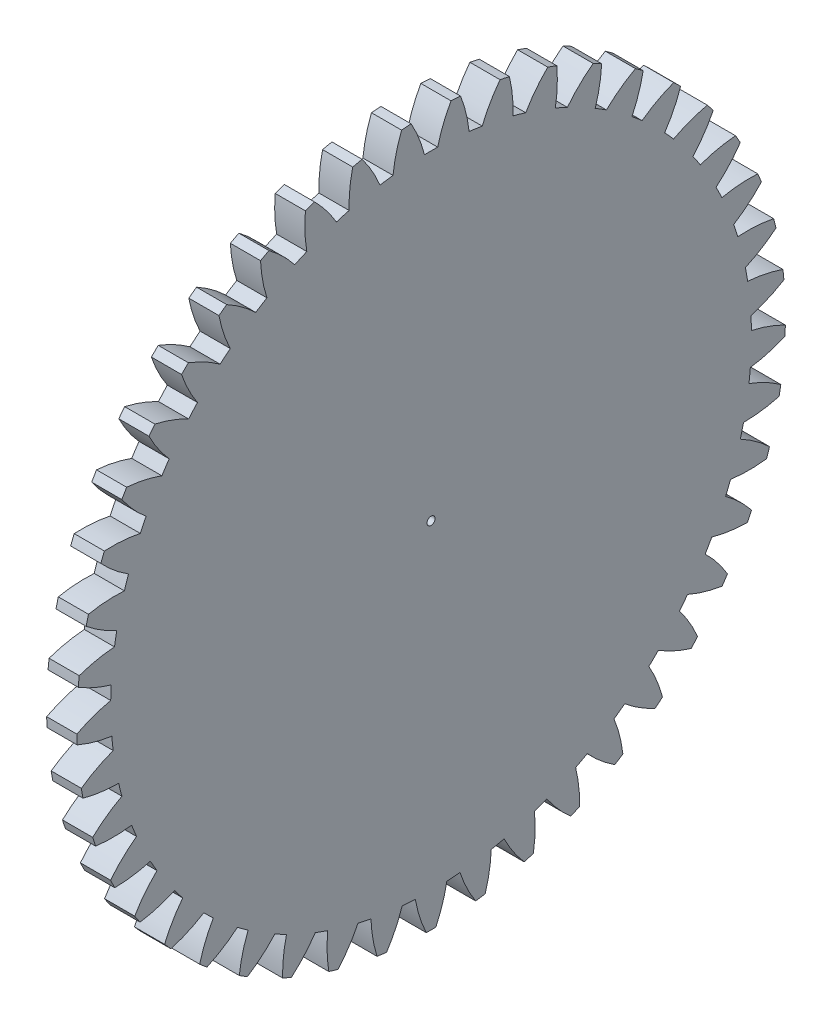
SolidWorks part; units mm, degrees
ref_plane "Plane1" through (0, 0, 0) normal (0, 0, 1) x (1, 0, 0)
ref_plane "Plane2" through (0, 0, 0) normal (0, 1, 0) x (1, 0, 0)
ref_plane "Plane3" through (0, 0, 0) normal (1, 0, 0) x (0, 0, -1)
sketch "HoldingSke" plane through (0, 0, 0) normal (0, 1, 0) x (1, 0, 0)
  line L0 (0, 0) -> (0.4714, -0.4714)
  line L1 (-15, 0) -> (100, 0) construction
  line L2 (0, 0) -> (-2.1039, 2.3779)
  line L3 (0, 0) -> (-11.863, 4.5341)
  line L4 (0, 0) -> (6.1066, 6.1066)
  line L5 (0, 0) -> (-46.8476, -17.4728)
  line L6 (0, 0) -> (-2.4869, -1.6779)
  line L7 (-2.1039, 2.3779) -> (8.6586, 51.2059)
  line L8 (-76.2, 54.61) -> (-76.1, 54.61)
  line L9 (-71.009, 38.7566) -> (-53.1078, 45.2721)
  line L10 (-76.2, 71.12) -> (104.1128, 71.12)
  line L11 (0, 0) -> (-3, 0)
  line L12 (-76.2, 101.6) -> (-76.147, 101.6)
  line L13 (24.9733, 27.94) -> (52.9518, 28.4284)
  line L14 (24.9733, 27.94) -> (24.9743, 27.94)
  line L15 (24.9733, 27.94) -> (100.4006, 29.5858)
  line L16 (-63.627, -1.5) -> (-12.827, -1.5)
  circle A0 centre (0, 0) radius 0.4
  circle A1 centre (0, 0) radius 31.874
  circle A2 centre (0, 0) radius 37.5
  circle A3 centre (0, 0) radius 0.4
  dimension "MHD" = 63.748
  dimension "Hub_dia" = 75
  dimension "Bore" = 0.8
  dimension "MBD" = 0.8
  dimension "Num_teeth" = 45
  dimension "Pitch" = 0.6667
  dimension "Overall_len" = 50
  dimension "Show_teeth" = 45
  dimension "Thickness" = 3
  dimension "OAL" = 50.0001
  dimension "T_dim" = 0.1
  dimension "Ap" = 20
  dimension "H" = 19.05
  dimension "Pitch_radius" = 180.3128
  dimension "Width" = 3
  dimension "Backlash" = 0.053
  dimension "Addendum_fac" = 1
  dimension "Dedendum_fac" = 1.25
  dimension "Clearance_fac" = 0.25
  dimension "Dedendum_add" = 0.001
  dimension "Module" = 1.5
sketch "BasProSke" plane through (0, 0, 0) normal (0, 1, 0) x (1, 0, 0)
  line L0 (-10, 0) -> (60, 0) construction
  line L1 (0, 0) -> (0, 35.25)
  line L2 (0, 0) -> (3, 0)
  line L3 (3, 0) -> (3, 35.25)
  line L4 (3, 35.25) -> (0, 35.25)
  dimension "Thickness" = 3
  dimension "Diameter" = 70.5
revolve "Base-Revolve" add sketch "BasProSke" angle 360 about L0
sketch "TooCutSke" plane through (0, 0, 0) normal (1, 0, 0) x (0, 0, -1)
  line L1 (0, 0) -> (0, 107) construction
  line L2 (0, 0) -> (-1.2706, 33.7261) construction
  line L3 (0, 0) -> (-4.7061, 67.3008) construction
  line L4 (-1.2706, 33.7261) -> (-2.3531, 33.6504) construction
  arc A0 (0.6574, 31.8672) -> (-0.6574, 31.8672) centre (0, 0) ccw
  arc A1 (1.9967, 35.2188) -> (-1.9967, 35.2188) centre (0, 0) ccw
  circle A2 centre (0, 0) radius 33.75 construction
  circle A3 centre (0, 0) radius 31.7146 construction
  arc A4 (-0.6574, 31.8672) -> (-1.9967, 35.2188) centre (-13.7507, 28.5786) ccw
  arc A5 (1.9967, 35.2188) -> (0.6574, 31.8672) centre (13.7507, 28.5786) ccw
  dimension "Root_dia" = 63.748
  dimension "Overcut_dia" = 70.5508
  dimension "Pitch_dia" = 67.5
  dimension "Base_dia" = 63.4293
  dimension "Flank_rad" = 13.5
  dimension "Half_ang" = 4
  dimension "Half_CT" = 1.0851
extrude "ToothCut" cut sketch "TooCutSke" along normal through all
fillet "Breaks" [suppressed] radius 0.03
fillet "RootFillets" [suppressed] radius 0.376
pattern_circular "TeethCuts" count 45 every 8 about axis through (-10, 0, 0) along (1, 0, 0) of "ToothCut", "RootFillets", "Breaks"
sketch "HubNeaOneSke" plane through (0, 0, 0) normal (-1, 0, 0) x (0, 0, 1)
  circle A0 centre (0, 0) radius 31.874
  dimension "Diameter" = 63.748
extrude "HubNearOne" [suppressed] add sketch "HubNeaOneSke" along normal blind 47.0001
sketch "HubNeaBotSke" plane through (0, 0, 0) normal (-1, 0, 0) x (0, 0, 1)
  circle A0 centre (0, 0) radius 31.874
  dimension "Diameter" = 63.748
extrude "HubNearBoth" [suppressed] add sketch "HubNeaBotSke" along normal blind 23.5
ref_plane "FarPln" through (3, 0, 0) normal (1, 0, 0) x (0, 0, -1)
sketch "HubFarSke" plane through (3, 0, 0) normal (1, 0, 0) x (0, 0, -1)
  circle A0 centre (0, 0) radius 31.874
  dimension "Diameter" = 63.748
extrude "HubFar" [suppressed] add sketch "HubFarSke" along normal blind 23.5
sketch "BorSke" plane through (0, 0, 0) normal (1, 0, 0) x (0, 0, -1)
  circle A0 centre (0, 0) radius 0.4
  dimension "Diameter" = 0.8
extrude "Bore" cut sketch "BorSke" along normal mid plane 100.0001
sketch "KeySke" plane through (0, 0, 0) normal (1, 0, 0) x (0, 0, -1)
  line L0 (-0.05, 0) -> (-0.05, 0.5)
  line L1 (-0.05, 0.5) -> (0.05, 0.5)
  line L2 (0.05, 0.5) -> (0.05, 0)
  line L3 (0, 0) -> (0, 34) construction
  line L4 (-0.05, 0) -> (0.05, 0)
  dimension "Offset" = 0.5
  dimension "Width" = 0.1
extrude "Keyway" [suppressed] cut sketch "KeySke" along normal mid plane 100.0001
pattern_circular "Keyway2" [suppressed] count 2 every 90 about axis through (-10, 0, 0) along (1, 0, 0)
equation "' \"Module@HoldingSke\" = 6.35"
equation "' \"Num_teeth@HoldingSke\" = 12"
equation "' \"Ap@HoldingSke\" =  20"
equation "' \"Ap@HoldingSke\" = 20"
equation "' \"Width@HoldingSke\" = 0.5 * 25.4"
equation "' \"Hub_dia@HoldingSke\"= 1 * 25.4"
equation "' \"Hub_dia@HoldingSke\" = 1 * 25.4"
equation "' \"Overall_len@HoldingSke\" = 1.0 * 25.4"
equation "' \"Bore@HoldingSke\" = 0.75 * 25.4"
equation "' \"T_dim@HoldingSke\" = 0.1 * 25.4"
equation "' \"Width@KeySke\" = 0.25 * 25.4"
equation "' \"Show_teeth@HoldingSke\" = 13"
equation "' \"Backlash@HoldingSke\" = 0.009 * 25.4"
equation "' \"Addendum_fac@HoldingSke\" = 1.0"
equation "' \"Dedendum_fac@HoldingSke\" = 1.25"
equation "' \"Dedendum_add@HoldingSke\" = 0.00005 * 25.4"
equation "' \"Clearance_fac@HoldingSke\" = 0.25"
equation "\"Pitch@HoldingSke\" = 1 / \"Module@HoldingSke\""
equation "\"Overcut_dia@TooCutSke\" = (\"Num_teeth@HoldingSke\" + 2 * \"Addendum_fac@HoldingSke\") / \"Pitch@HoldingSke\" + 0.002 * 25.4"
equation "\"Pitch_dia@TooCutSke\" = \"Num_teeth@HoldingSke\" / \"Pitch@HoldingSke\""
equation "\"Base_dia@TooCutSke\" = \"Num_teeth@HoldingSke\" / \"Pitch@HoldingSke\" * cos((\"Ap@HoldingSke\"  * 3.14159265 / 180))"
equation "\"Root_dia@TooCutSke\" = (\"Num_teeth@HoldingSke\" + 2) / \"Pitch@HoldingSke\" - 2 * (\"Addendum_fac@HoldingSke\" + \"Dedendum_fac@HoldingSke\") / \"Pitch@HoldingSke\" - \"Dedendum_add@HoldingSke\" * 2"
equation "\"Half_ang@TooCutSke\" = 180 / \"Num_teeth@HoldingSke\""
equation "\"Half_CT@TooCutSke\" = \"Num_teeth@HoldingSke\" / \"Pitch@HoldingSke\" * sin((3.14159265 / 2 / \"Num_teeth@HoldingSke\")) / 2 - 7 * \"Backlash@HoldingSke\" / 4"
equation "\"Flank_rad@TooCutSke\" = \"Num_teeth@HoldingSke\" / \"Pitch@HoldingSke\" / 5"
equation "\"Radius@RootFillets\" = \"Clearance_fac@HoldingSke\" / \"Pitch@HoldingSke\" + \"Dedendum_add@HoldingSke\""
equation "\"Break_rad@Breaks\" = 0.02 / \"Pitch@HoldingSke\""
equation "\"Thickness@HoldingSke\" = \"Width@HoldingSke\""
equation "\"OAL@HoldingSke\" = \"Thickness@HoldingSke\""
equation "\"MHD@HoldingSke\" = (\"Num_teeth@HoldingSke\" + 2) / \"Pitch@HoldingSke\" - 2 * (\"Addendum_fac@HoldingSke\" + \"Dedendum_fac@HoldingSke\")  / \"Pitch@HoldingSke\" - \"Dedendum_add@HoldingSke\" * 2"
equation "\"MBD@HoldingSke\" = (\"Num_teeth@HoldingSke\" + 2) / \"Pitch@HoldingSke\" - 2 * (\"Addendum_fac@HoldingSke\" + \"Dedendum_fac@HoldingSke\")  / \"Pitch@HoldingSke\" - \"Dedendum_add@HoldingSke\" * 2 - 0.002 * 25.4"
equation "\"MHD@HoldingSke\" = ((sgn( \"MHD@HoldingSke\" - \"Hub_dia@HoldingSke\" )-1)*( \"MHD@HoldingSke\" - \"Hub_dia@HoldingSke\" ))/-2+ \"Hub_dia@HoldingSke\""
equation "\"MBD@HoldingSke\" = ((sgn( \"MBD@HoldingSke\" - \"Bore@HoldingSke\" )-1)*( \"MBD@HoldingSke\" - \"Bore@HoldingSke\" ))/-2+ \"Bore@HoldingSke\""
equation "\"OAL@HoldingSke\" = ((sgn( \"OAL@HoldingSke\" - \"Overall_len@HoldingSke\" )+1)*( \"OAL@HoldingSke\" - \"Overall_len@HoldingSke\" ))/2 + \"Overall_len@HoldingSke\" + 0.000002 * 25.4"
equation "\"Num_teeth@TeethCuts\" = int( \"Show_teeth@HoldingSke\" ) + 1"
equation "\"Num_teeth@TeethCuts\" = ((sgn( \"Num_teeth@TeethCuts\" - \"Num_teeth@HoldingSke\" )-1)*( \"Num_teeth@TeethCuts\" - \"Num_teeth@HoldingSke\" ))/-2+ \"Num_teeth@HoldingSke\""
equation "\"Num_teeth@TeethCuts\" = ((sgn( \"Num_teeth@TeethCuts\" - 2.0)+1)*( \"Num_teeth@TeethCuts\" - 2.0))/2 +2.0"
equation "\"Angle@TeethCuts\" = 360.0 / \"Num_teeth@HoldingSke\""
equation "\"Diameter@BasProSke\" = (\"Num_teeth@HoldingSke\" + 2 * \"Addendum_fac@HoldingSke\") / \"Pitch@HoldingSke\""
equation "\"Thickness@BasProSke\"  = \"Thickness@HoldingSke\""
equation "' \"Fillet_rad@BasProSke\" =  \"Thickness@HoldingSke\" * 0.05"
equation "' \"Fillet_rad@BasProSke\" = \"Thickness@HoldingSke\" * 0.05"
equation "\"MHD@HoldingSke\" = ((sgn( \"MHD@HoldingSke\" - \"Root_dia@TooCutSke\" )-1)*( \"MHD@HoldingSke\" - \"Root_dia@TooCutSke\" ))/-2+ \"Root_dia@TooCutSke\""
equation "\"Diameter@HubNeaOneSke\" = \"MHD@HoldingSke\""
equation "\"Length@HubNearOne\" = \"OAL@HoldingSke\" - \"Thickness@BasProSke\""
equation "\"Diameter@HubNeaBotSke\" = \"MHD@HoldingSke\""
equation "\"Length@HubNearBoth\" = ( \"OAL@HoldingSke\" - \"Thickness@BasProSke\" ) / 2.0"
equation "\"Thickness@FarPln\" = \"Thickness@BasProSke\""
equation "\"Diameter@HubFarSke\" = \"MHD@HoldingSke\""
equation "\"Length@HubFar\" = ( \"OAL@HoldingSke\" - \"Thickness@BasProSke\" ) / 2.0"
equation "\"Diameter@BorSke\" = \"MBD@HoldingSke\""
equation "\"D1@Bore\" = \"OAL@HoldingSke\" * 2.0"
equation "\"D1@Keyway\" = \"OAL@HoldingSke\" * 2.0"
equation "\"Offset@KeySke\" = \"T_dim@HoldingSke\" + \"MBD@HoldingSke\" / 2.0"
